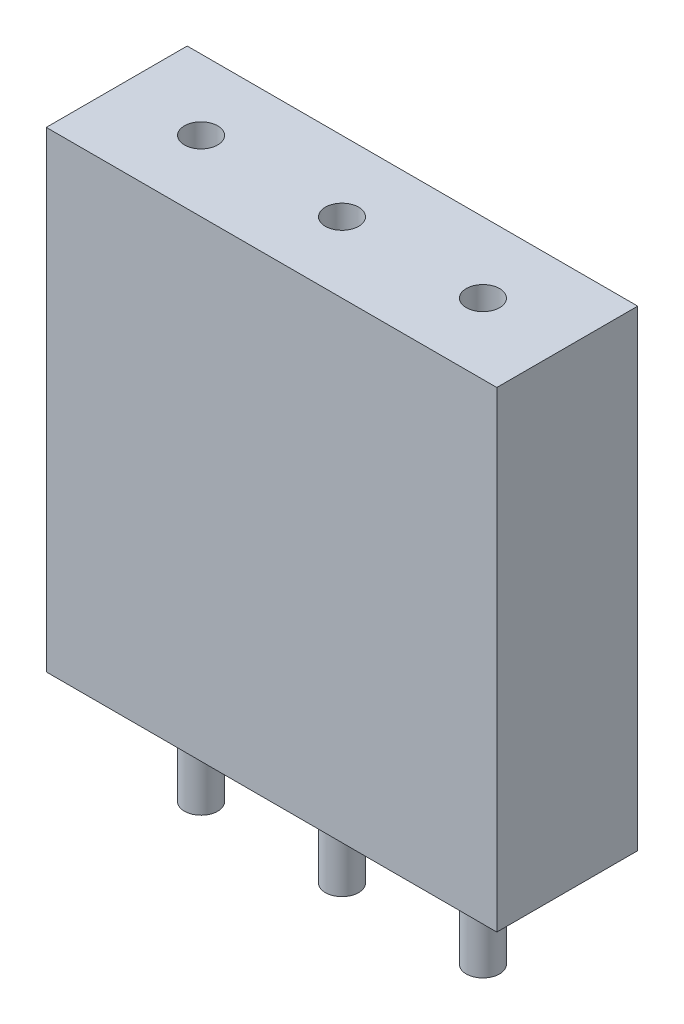
SolidWorks part; units mm, degrees
ref_plane "Спереди" through (0, 0, 0) normal (0, 0, 1) x (1, 0, 0)
ref_plane "Сверху" through (0, 0, 0) normal (0, 1, 0) x (1, 0, 0)
ref_plane "Справа" through (0, 0, 0) normal (1, 0, 0) x (0, 0, -1)
sketch "Эскиз1" plane through (0, 0, 0) normal (0, 1, 0) x (1, 0, 0)
  line L1 (-4.06, 1.27) -> (4.06, 1.27)
  line L2 (-4.06, 1.27) -> (-4.06, -1.27)
  line L3 (-4.06, -1.27) -> (4.06, -1.27)
  line L4 (4.06, 1.27) -> (4.06, -1.27)
  line L5 (-4.06, 1.27) -> (4.06, -1.27) construction
  line L6 (-4.06, -1.27) -> (4.06, 1.27) construction
  point P0 (0, 0)
extrude "Бобышка-Вытянуть1" add sketch "Эскиз1" along normal blind 8.5
sketch "Эскиз2" plane through (0, 8.5, 0) normal (0, 1, 0) x (1, 0, 0)
  circle A2 centre (-2.54, 0) radius 0.3
  circle A3 centre (0, 0) radius 0.3
  circle A4 centre (2.54, 0) radius 0.3
extrude "Вырез-Вытянуть1" cut sketch "Эскиз2" against normal blind 8.5
sketch "Эскиз3" plane through (0, 0, 0) normal (0, -1, 0) x (1, 0, 0)
  circle A2 centre (-2.54, 0) radius 0.3
  circle A3 centre (0, 0) radius 0.3
  circle A4 centre (2.54, 0) radius 0.3
extrude "Бобышка-Вытянуть2" add sketch "Эскиз3" along normal blind 1.9 separate body
ref_plane "Плоскость1" through (0, 0, 0) normal (0, 0, 1) x (1, 0, 0)
